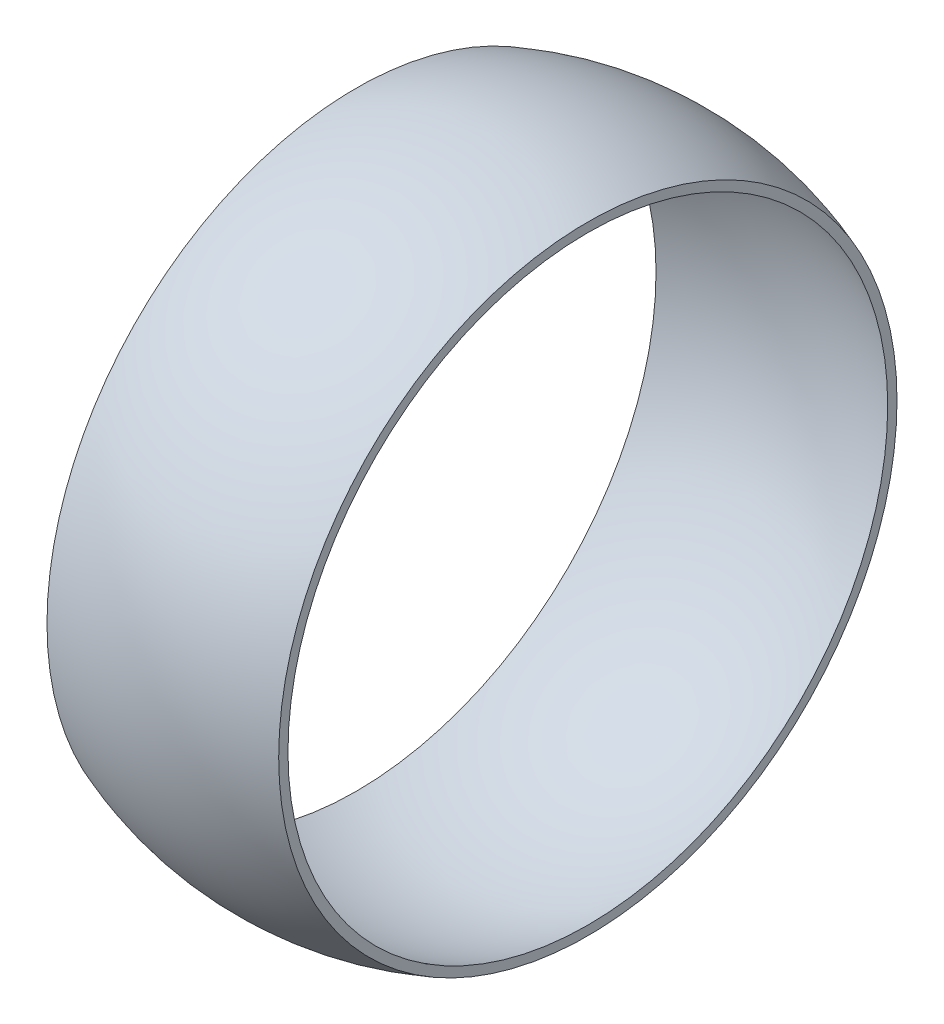
SolidWorks part; units mm, degrees
material "PTFE (general)"
ref_plane "Front Plane" through (0, 0, 0) normal (0, 0, 1) x (1, 0, 0)
ref_plane "Top Plane" through (0, 0, 0) normal (0, 1, 0) x (1, 0, 0)
ref_plane "Right Plane" through (0, 0, 0) normal (1, 0, 0) x (0, 0, -1)
sketch "Sketch1" plane through (0, 0, 0) normal (0, 0, 1) x (1, 0, 0)
  line L0 (0, 0) -> (-35.4366, 0) construction
  line L1 (0, 0) -> (0, 6.05) construction
  line L2 (-4, 10.6752) -> (-4, 10.3542)
  line L3 (4, 10.6752) -> (4, 10.3542)
  arc A0 (4, 10.3542) -> (-4, 10.3542) centre (0, 0) ccw
  arc A1 (4, 10.6752) -> (-4, 10.6752) centre (0, 0) ccw
  dimension "D1" = 11.1
  dimension "D2" = 11.4
  dimension "D3" = 8
revolve "Revolve1" add sketch "Sketch1" angle 360 about L0
